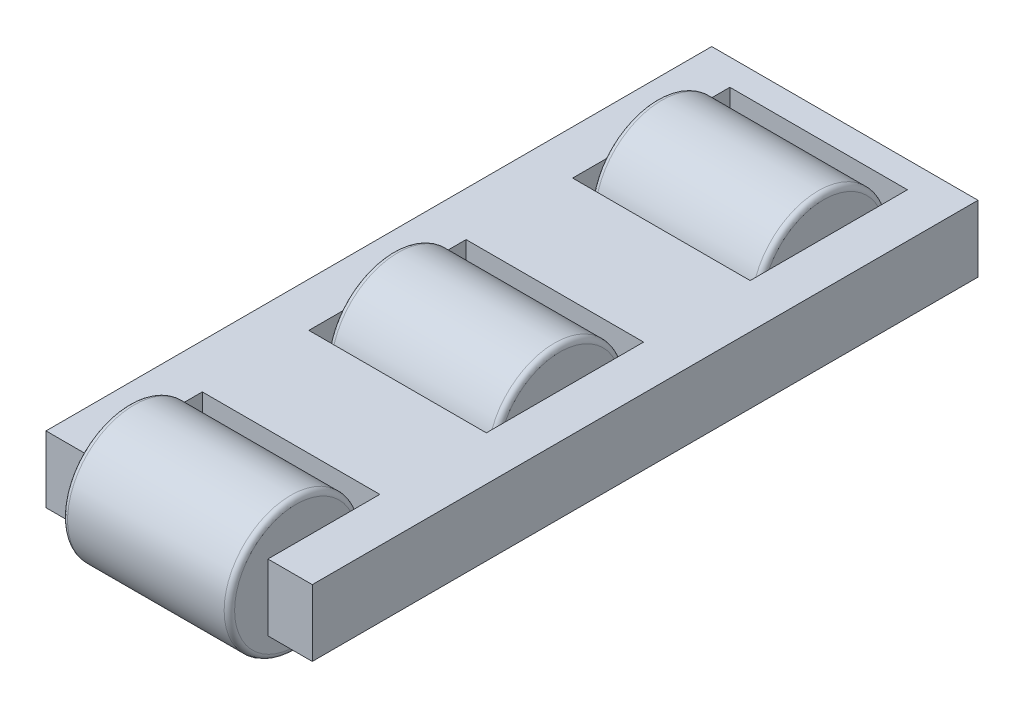
SolidWorks part; units mm, degrees
ref_plane "Front Plane" through (0, 0, 0) normal (0, 0, 1) x (1, 0, 0)
ref_plane "Top Plane" through (0, 0, 0) normal (0, 1, 0) x (1, 0, 0)
ref_plane "Right Plane" through (0, 0, 0) normal (1, 0, 0) x (0, 0, -1)
sketch "Sketch1" plane through (0, 0, 0) normal (0, 1, 0) x (1, 0, 0)
  line L1 (-25.4, -63.5) -> (25.4, -63.5)
  line L2 (-25.4, -63.5) -> (-25.4, 63.5)
  line L3 (-25.4, 63.5) -> (25.4, 63.5)
  line L4 (25.4, -63.5) -> (25.4, 63.5)
  line L5 (-25.4, -63.5) -> (25.4, 63.5) construction
  line L6 (-25.4, 63.5) -> (25.4, -63.5) construction
  point P0 (0, 0)
  dimension "D1" = 127
  dimension "D2" = 50.8
extrude "Boss-Extrude1" add sketch "Sketch1" along normal blind 12.7
sketch "Sketch2" plane through (25.4, 0, 0) normal (1, 0, 0) x (0, 0, -1)
  line L0 (-63.5, 12.7) -> (63.5, 12.7) construction
  line L1 (-63.5, 0) -> (-50.8, 0) construction
  line L2 (-63.5, 0) -> (-63.5, 12.7) construction
  line L3 (-63.5, 12.7) -> (-50.8, 12.7) construction
  line L4 (-50.8, 0) -> (-50.8, 12.7) construction
  line L5 (-63.5, 0) -> (-50.8, 12.7) construction
  line L6 (43.5, 9.8912) -> (63.5, 9.8912) construction
  line L7 (63.5, 12.7) -> (63.5, 0) construction
  line L8 (-57.15, 9.8912) -> (-77.15, 9.8912) construction
  line L9 (-6.825, 12.7) -> (-6.825, 0) construction
  line L10 (-63.5, 0) -> (63.5, 0) construction
  line L11 (43.5, 12.7) -> (43.5, 0) construction
  line L12 (-57.15, 6.35) -> (-6.825, 6.35) construction
  line L13 (-6.825, 6.35) -> (43.5, 6.35) construction
  circle A0 centre (-6.825, 6.35) radius 12.7
  circle A1 centre (43.5, 6.35) radius 12.7
  circle A2 centre (-57.15, 6.35) radius 12.7
  point P13 (-6.825, 6.35)
  point P14 (43.5, 6.35)
  point P18 (-57.15, 6.35)
  dimension "D1" = 25.4
  dimension "D2" = 20
sketch "Sketch3" plane through (0, 12.7, 0) normal (0, 1, 0) x (1, 0, 0)
  line L0 (-25.4, -63.5) -> (-12.7, -63.5) construction
  line L1 (-25.4, -63.5) -> (25.4, -63.5) construction
  line L2 (-12.7, -63.5) -> (0, -63.5) construction
  line L3 (0, -63.5) -> (12.7, -63.5) construction
  line L4 (12.7, -63.5) -> (25.4, -63.5) construction
  line L5 (-25.4, -63.5) -> (-16.9333, -63.5) construction
  line L6 (-16.9333, -63.5) -> (-8.4667, -63.5) construction
  line L7 (-8.4667, -63.5) -> (0, -63.5) construction
  line L8 (0, -63.5) -> (8.4667, -63.5) construction
  line L9 (8.4667, -63.5) -> (16.9333, -63.5) construction
  line L10 (16.9333, -63.5) -> (25.4, -63.5) construction
  line L11 (-16.9333, -63.5) -> (-16.9333, -42.15)
  line L12 (16.9333, -63.5) -> (16.9333, -42.15)
  line L13 (16.9333, -42.15) -> (-16.9333, -42.15)
  line L14 (-16.9333, -63.5) -> (16.9333, -63.5)
  line L15 (-16.9333, 8.175) -> (16.9333, 8.175)
  line L16 (-16.9333, 8.175) -> (-16.9333, -21.825)
  line L17 (-16.9333, -21.825) -> (16.9333, -21.825)
  line L18 (16.9333, 8.175) -> (16.9333, -21.825)
  line L19 (16.9333, 28.5) -> (-16.9333, 28.5)
  line L20 (16.9333, 28.5) -> (16.9333, 58.5)
  line L21 (16.9333, 58.5) -> (-16.9333, 58.5)
  line L22 (-16.9333, 28.5) -> (-16.9333, 58.5)
  point P30 (16.9333, -6.825)
  point P32 (16.9333, 43.5)
  dimension "D1" = 15
  dimension "D2" = 30
extrude "Cut-Extrude1" cut sketch "Sketch3" against normal up to surface (12.7 mm away) up to face at (0, 0, 0)
sketch "Sketch4" plane through (0, 12.7, 0) normal (0, 1, 0) x (1, 0, 0)
  line L0 (12.5526, 28.5) -> (12.5526, 8.175) construction
  line L1 (-16.9333, 28.5) -> (16.9333, 28.5) construction
  line L2 (16.9333, 8.175) -> (-16.9333, 8.175) construction
  line L3 (25.4, -6.825) -> (25.4, 43.5) construction
  line L4 (25.4, 5.6375) -> (17.78, 5.6375)
  line L5 (25.4, 5.6375) -> (25.4, 31.0375)
  line L6 (25.4, 31.0375) -> (17.78, 31.0375)
  line L7 (17.78, 5.6375) -> (17.78, 31.0375)
  line L8 (25.4, 5.6375) -> (17.78, 31.0375) construction
  line L9 (25.4, 31.0375) -> (17.78, 5.6375) construction
  line L10 (9.0274, -21.825) -> (9.0274, -42.15) construction
  line L11 (17.78, -44.6875) -> (25.4, -44.6875)
  line L12 (17.78, -44.6875) -> (17.78, -19.2875)
  line L13 (17.78, -19.2875) -> (25.4, -19.2875)
  line L14 (25.4, -44.6875) -> (25.4, -19.2875)
  line L15 (17.78, -44.6875) -> (25.4, -19.2875) construction
  line L16 (17.78, -19.2875) -> (25.4, -44.6875) construction
  line L17 (-16.9333, -21.825) -> (16.9333, -21.825) construction
  line L18 (16.9333, -42.15) -> (-16.9333, -42.15) construction
  line L19 (25.4, -57.15) -> (25.4, -6.825) construction
  point P6 (9.0274, -31.9875)
  point P7 (21.59, 18.3375)
  point P12 (12.5526, 18.3375)
  point P16 (21.59, -31.9875)
  dimension "D1" = 7.62
  dimension "D2" = 25.4
ref_plane "Plane1" through (15.9333, 0, 0) normal (-1, 0, 0) x (0, 0, 1)
ref_plane "Plane2" through (-15.9333, 0, 0) normal (1, 0, 0) x (0, 0, -1)
sketch "Sketch5" plane through (15.9333, 0, 0) normal (-1, 0, 0) x (0, 0, 1)
  circle A0 centre (6.825, 6.35) radius 12.7
  circle A1 centre (6.825, 6.35) radius 12.7 construction
  circle A2 centre (-43.5, 6.35) radius 12.7
  circle A3 centre (57.15, 6.35) radius 12.7
extrude "Boss-Extrude2" add sketch "Sketch5" along normal up to surface (31.8667 mm away) separate body up to plane "Plane2"
fillet "Fillet1" radius 1 2 edges at (-15.9333, 6.35, -5.875) (15.9333, 6.35, 19.525)
fillet "Fillet2" radius 1 2 edges at (15.9333, 6.35, -30.8) (-15.9333, 6.35, -56.2)
fillet "Fillet3" radius 1 2 edges at (15.9333, 6.35, 69.85) (-15.9333, 6.35, 44.45)
sketch "Sketch6" plane through (0, 12.7, 0) normal (0, 1, 0) x (1, 0, 0)
  line L0 (0, 28.5) -> (0, 8.175) construction
  line L1 (-16.9333, 28.5) -> (16.9333, 28.5) construction
  line L2 (16.9333, 8.175) -> (-16.9333, 8.175) construction
  line L3 (0, -21.825) -> (0, -42.15) construction
  line L4 (-16.9333, -21.825) -> (16.9333, -21.825) construction
  line L5 (16.9333, -42.15) -> (-16.9333, -42.15) construction
  line L7 (16.9333, 28.5) -> (16.9333, 58.5) construction
  line L8 (-16.9333, 58.5) -> (-16.9333, 28.5) construction
  circle A0 centre (16.9333, 18.3375) radius 1.5
  circle A1 centre (-16.9333, 18.3375) radius 1.5
  circle A2 centre (16.9333, -31.9875) radius 1.5
  circle A3 centre (-16.9333, -31.9875) radius 1.5
  point P9 (0, 18.3375)
  point P22 (0, -31.9875)
  dimension "D1" = 3
